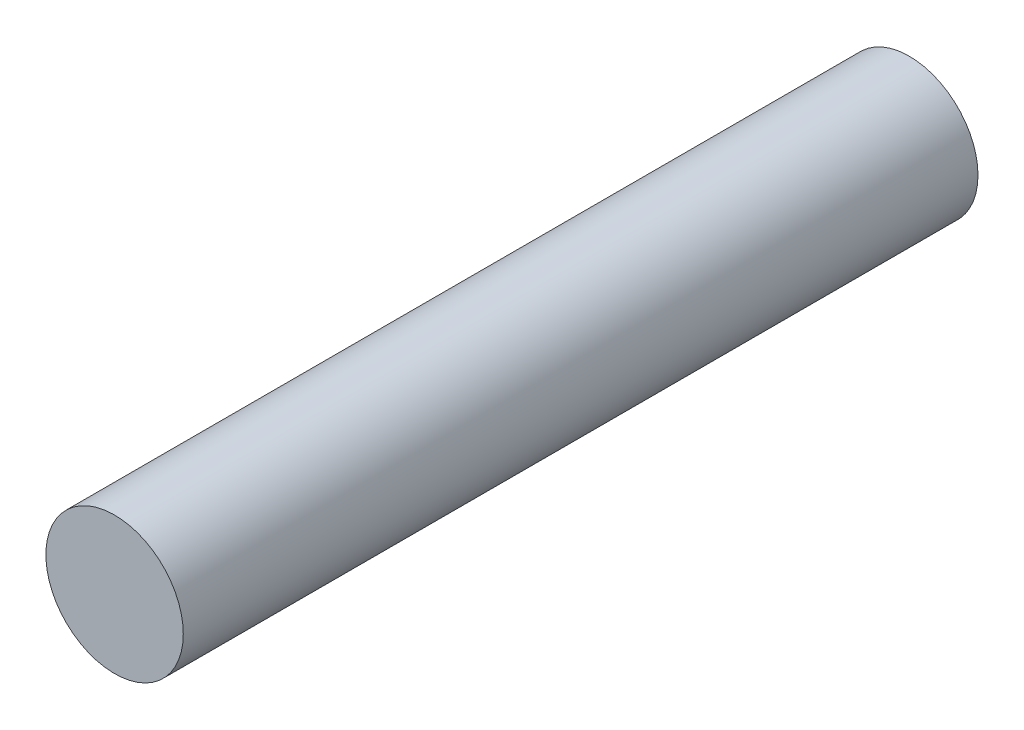
SolidWorks part; units mm, degrees
ref_plane "Front Plane" through (0, 0, 0) normal (0, 0, 1) x (1, 0, 0)
ref_plane "Top Plane" through (0, 0, 0) normal (0, 1, 0) x (1, 0, 0)
ref_plane "Right Plane" through (0, 0, 0) normal (1, 0, 0) x (0, 0, -1)
sketch "Sketch1" plane through (0, 0, 0) normal (0, 0, 1) x (1, 0, 0)
  circle A0 centre (0, 0) radius 155
extrude "Boss-Extrude1" add sketch "Sketch1" along normal blind 627 and the other way blind 1165.9182 contours A0
scale "Scale1" bodies to scale 101 scale about centroid uniform scaling yes scale factor 0.3
